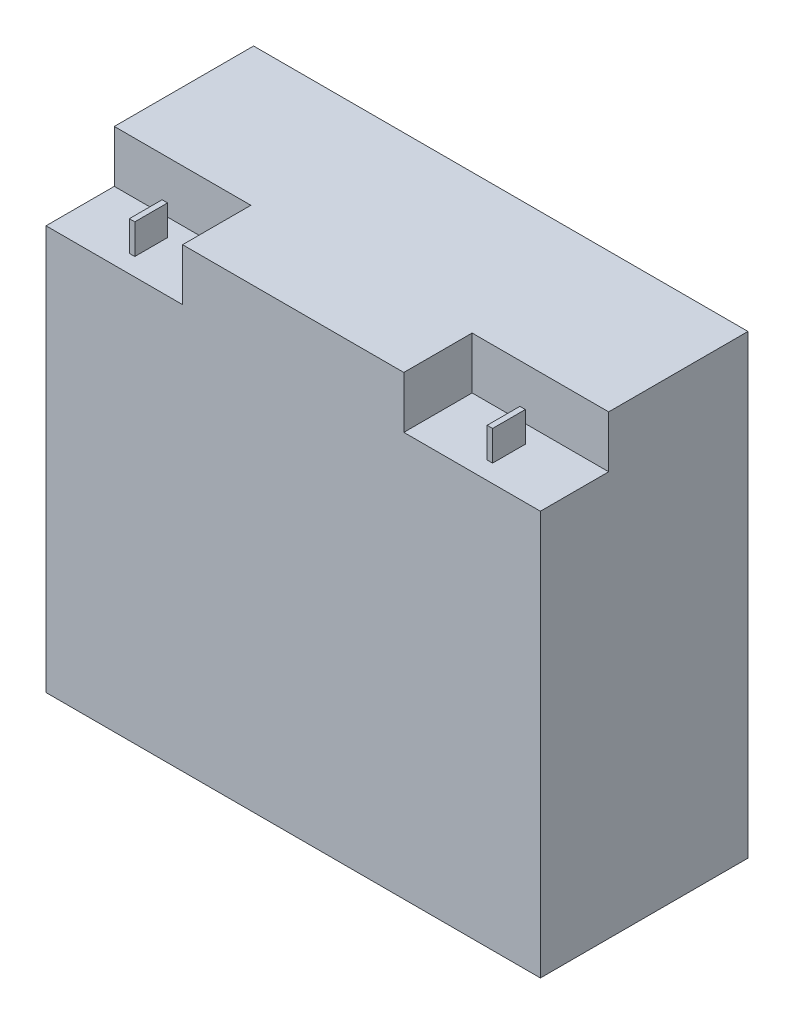
SolidWorks part; units mm, degrees
material "ALUMINUM 6061-T6"
ref_plane "Front Plane" through (0, 0, 0) normal (0, 0, 1) x (1, 0, 0)
ref_plane "Top Plane" through (0, 0, 0) normal (0, 1, 0) x (1, 0, 0)
ref_plane "Right Plane" through (0, 0, 0) normal (1, 0, 0) x (0, 0, -1)
sketch "Sketch1" plane through (0, 0, 0) normal (0, 0, 1) x (1, 0, 0)
  line L1 (-90.5, -83.5) -> (90.5, -83.5)
  line L2 (-90.5, -83.5) -> (-90.5, 83.5)
  line L3 (-90.5, 83.5) -> (90.5, 83.5)
  line L4 (90.5, -83.5) -> (90.5, 83.5)
  line L5 (-90.5, -83.5) -> (90.5, 83.5) construction
  line L6 (-90.5, 83.5) -> (90.5, -83.5) construction
  point P0 (0, 0)
  dimension "D1" = 181
  dimension "D2" = 167
extrude "Boss-Extrude1" add sketch "Sketch1" along normal mid plane 76
sketch "Sketch2" plane through (0, 0, 38) normal (0, 0, 1) x (1, 0, 0)
  text T0 "ES17-12" font "Century Gothic" height 20
sketch "Sketch3" plane through (0, 0, 38) normal (0, 0, 1) x (1, 0, 0)
  line L1 (-90.5, 83.5) -> (-40.5, 83.5)
  line L2 (-90.5, 83.5) -> (-90.5, 64.5)
  line L3 (-90.5, 64.5) -> (-40.5, 64.5)
  line L4 (-40.5, 83.5) -> (-40.5, 64.5)
  line L5 (90.5, 83.5) -> (40.5, 83.5)
  line L6 (90.5, 83.5) -> (90.5, 64.5)
  line L7 (90.5, 64.5) -> (40.5, 64.5)
  line L8 (40.5, 83.5) -> (40.5, 64.5)
  dimension "D1" = 19
  dimension "D2" = 50
  dimension "D3" = 19
  dimension "D4" = 50
extrude "Cut-Extrude1" cut sketch "Sketch3" against normal blind 25
sketch "Sketch4" plane through (0, 64.5, 0) normal (0, 1, 0) x (1, 0, 0)
  line L0 (-65.5, -31.5) -> (-65.5, -38) construction
  line L1 (-66.5, -19.5) -> (-64.5, -19.5)
  line L2 (-66.5, -19.5) -> (-66.5, -31.5)
  line L3 (-66.5, -31.5) -> (-64.5, -31.5)
  line L4 (-64.5, -19.5) -> (-64.5, -31.5)
  line L5 (64.5, -19.5) -> (66.5, -19.5)
  line L6 (64.5, -19.5) -> (64.5, -31.5)
  line L7 (64.5, -31.5) -> (66.5, -31.5)
  line L8 (66.5, -19.5) -> (66.5, -31.5)
  line L9 (-90.5, -38) -> (-40.5, -38) construction
  line L10 (65.5, -31.5) -> (65.5, -38) construction
  line L11 (40.5, -38) -> (90.5, -38) construction
  line L12 (-65.5, -19.5) -> (-65.5, -13) construction
  line L13 (-90.5, -13) -> (-40.5, -13) construction
  dimension "D1" = 2
  dimension "D2" = 12
extrude "Boss-Extrude2" add sketch "Sketch4" along normal blind 11
